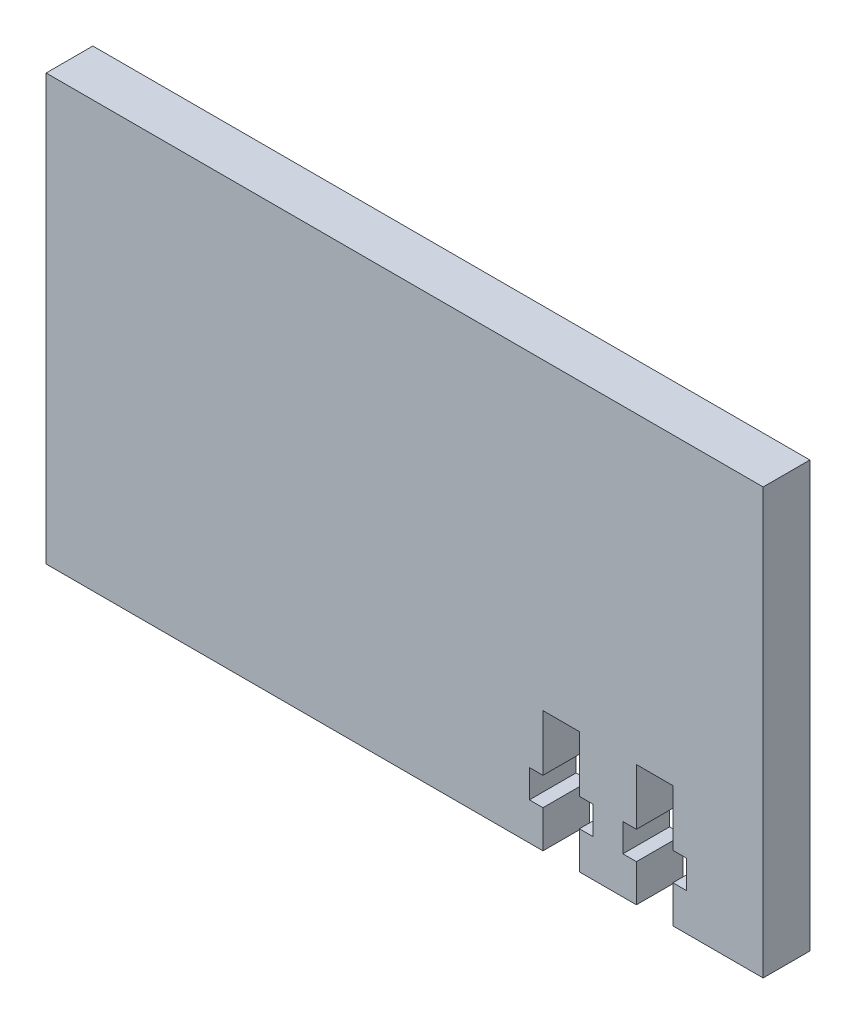
SolidWorks part; units mm, degrees
ref_plane "Front Plane" through (0, 0, 0) normal (0, 0, 1) x (1, 0, 0)
ref_plane "Top Plane" through (0, 0, 0) normal (0, 1, 0) x (1, 0, 0)
ref_plane "Right Plane" through (0, 0, 0) normal (1, 0, 0) x (0, 0, -1)
sketch "Sketch2" plane through (0, 0, 0) normal (0, 0, -1) x (-1, 0, 0)
  line L0 (222.9957, -9.5) -> (222.9957, -55)
  line L1 (222.9957, -9.5) -> (146.2775, -9.5)
  line L2 (222.9957, -55) -> (146.2775, -55)
  line L3 (146.2775, -9.5) -> (146.2775, -55)
  dimension "D1" = 45.5
  dimension "D2" = 76.7182
extrude "Boss-Extrude1" add sketch "Sketch2" along normal blind 5
sketch "Sketch3" plane through (0, 0, -5) normal (0, 0, -1) x (-1, 0, 0)
  line L0 (155.9375, -55) -> (159.8375, -55) construction
  line L1 (155.9375, -55) -> (155.9375, -51)
  line L2 (157.8875, -55) -> (157.8875, -42) construction
  line L3 (155.9375, -42) -> (159.8375, -42)
  line L4 (155.9375, -48) -> (154.4875, -48)
  line L5 (154.4875, -48) -> (154.4875, -51)
  line L6 (155.9375, -51) -> (154.4875, -51)
  line L7 (155.9375, -48) -> (155.9375, -42)
  line L8 (159.8375, -48) -> (159.8375, -42)
  line L9 (159.8375, -51) -> (161.2875, -51)
  line L10 (161.2875, -48) -> (161.2875, -51)
  line L11 (159.8375, -48) -> (161.2875, -48)
  line L12 (159.8375, -55) -> (159.8375, -51)
  line L13 (165.9375, -55) -> (169.8375, -55) construction
  line L14 (165.9375, -55) -> (165.9375, -51)
  line L15 (167.8875, -55) -> (167.8875, -42) construction
  line L16 (165.9375, -42) -> (169.8375, -42)
  line L17 (165.9375, -48) -> (164.4875, -48)
  line L18 (164.4875, -48) -> (164.4875, -51)
  line L19 (165.9375, -51) -> (164.4875, -51)
  line L20 (165.9375, -48) -> (165.9375, -42)
  line L21 (169.8375, -48) -> (169.8375, -42)
  line L22 (169.8375, -51) -> (171.2875, -51)
  line L23 (171.2875, -48) -> (171.2875, -51)
  line L24 (169.8375, -48) -> (171.2875, -48)
  line L25 (169.8375, -55) -> (169.8375, -51)
  line L26 (162.8875, 11.7401) -> (162.8875, -89.703) construction
  line L27 (165.9375, -55) -> (169.8375, -55)
  line L29 (155.9375, -55) -> (159.8375, -55)
  line L31 (146.2775, -55) -> (222.9957, -55) construction
  line L32 (146.2775, -9.5) -> (146.2775, -55) construction
  point P2 (0, 0)
  point P31 (0, 0)
  point P32 (152.8319, -39.1641)
  point P33 (0, 0)
  point P34 (0, 0)
  point P35 (0, 0)
  point P36 (0, 0)
  point P37 (0, 0)
  point P38 (0, 0)
  point P39 (156.7036, -38.8333)
  point P40 (0, 0)
  point P42 (0, 0)
  point P44 (158.8922, -55)
  dimension "D1" = 3.9
  dimension "D2" = 4
  dimension "D3" = 6
  dimension "D4" = 3
  dimension "D5" = 1.45
  dimension "D6" = 3.9
  dimension "D7" = 4
  dimension "D8" = 6
  dimension "D9" = 3
  dimension "D10" = 1.45
  dimension "D11" = 10
  dimension "D12" = 11.61
extrude "Cut-Extrude1" cut sketch "Sketch3" against normal blind 10
